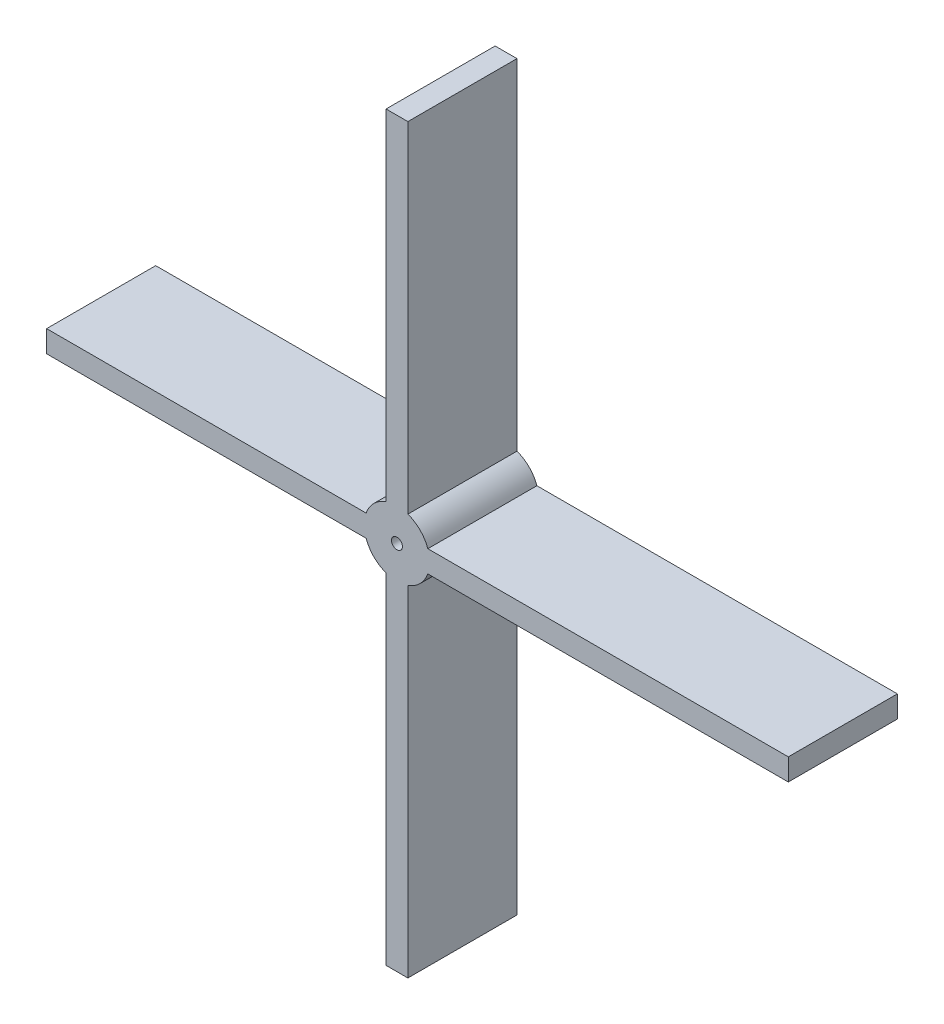
SolidWorks part; units mm, degrees
ref_plane "Front Plane" through (0, 0, 0) normal (0, 0, 1) x (1, 0, 0)
ref_plane "Top Plane" through (0, 0, 0) normal (0, 1, 0) x (1, 0, 0)
ref_plane "Right Plane" through (0, 0, 0) normal (1, 0, 0) x (0, 0, -1)
sketch "Sketch1" plane through (0, 0, 0) normal (0, 0, 1) x (1, 0, 0)
  line L1 (-160.6057, 5) -> (-5, 5)
  line L2 (-160.6057, 5) -> (-160.6057, -5)
  line L3 (-160.6057, -5) -> (-5, -5)
  line L4 (179.3943, 5) -> (179.3943, -5)
  line L5 (-5, -5) -> (5, 5) construction
  line L7 (-5, 170) -> (5, 170)
  line L8 (-5, 170) -> (-5, 5)
  line L9 (-5, -170) -> (5, -170)
  line L10 (5, 170) -> (5, 5)
  line L14 (-5, -5) -> (-5, -170)
  line L17 (5, -5) -> (5, -170)
  line L19 (5, -5) -> (179.3943, -5)
  line L20 (5, 5) -> (179.3943, 5)
  point P0 (0, 0)
  point P6 (-39.0277, -19.6193)
  point P13 (0, 0)
  dimension "D1" = 340
  dimension "D2" = 10
  dimension "D3" = 340
  dimension "D4" = 179.3943
  dimension "D5" = 39.0277
  dimension "D6" = 19.6193
extrude "Boss-Extrude2" add sketch "Sketch1" along normal blind 50
sketch "Sketch2" plane through (0, 0, 0) normal (0, 0, -1) x (-1, 0, 0)
  circle A0 centre (0, 0) radius 15
  dimension "D1" = 30
extrude "Boss-Extrude3" add sketch "Sketch2" against normal up to surface (50 mm away) up to face at (3.1314, 0, 50)
hole_wizard "Ø5.0 (5) Diameter Hole1" positions "Sketch3" profile "Sketch4" hole size "Ø5.0" standard "ANSI Metric" end condition through all
sketch "Sketch3" plane through (0, 0, 50) normal (0, 0, 1) x (1, 0, 0)
  point P0 (0, 0)
sketch "Sketch4" plane through (0, 0, 50) normal (1, 0, 0) x (0, -1, 0)
  line L0 (0, 0) -> (0, 50)
  line L1 (0, 50) -> (2.5, 50)
  line L2 (2.5, 50) -> (2.5, 0)
  line L5 (2.5, 0) -> (0, 0)
  line L11 (0, -6.35) -> (0, 107.95) construction
  dimension "Thru Hole Dia." = 5
  dimension "Thru Hole Depth" = 50
